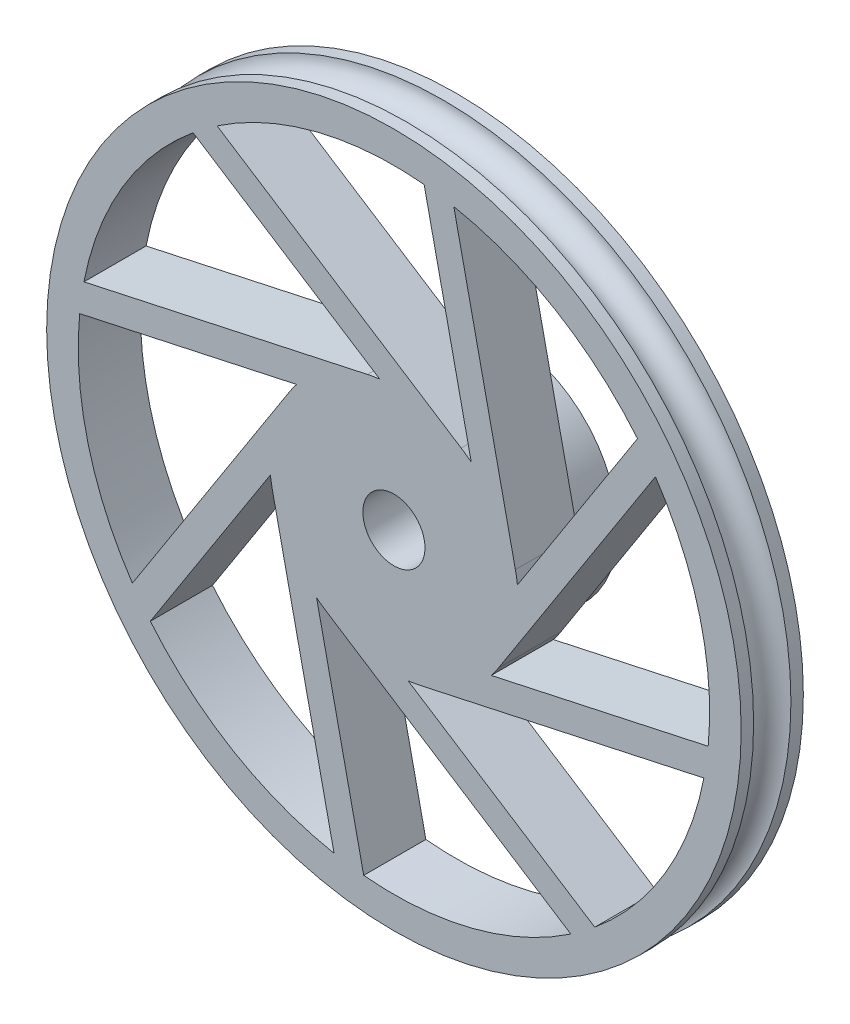
SolidWorks part; units mm, degrees
ref_plane "Front Plane" through (0, 0, 0) normal (0, 0, 1) x (1, 0, 0)
ref_plane "Top Plane" through (0, 0, 0) normal (0, 1, 0) x (1, 0, 0)
ref_plane "Right Plane" through (0, 0, 0) normal (1, 0, 0) x (0, 0, -1)
sketch "Sketch1" plane through (0, 0, 0) normal (0, 0, 1) x (1, 0, 0)
  circle A0 centre (0, 0) radius 27.94
  dimension "D1" = 55.88
extrude "Boss-Extrude1" add sketch "Sketch1" against normal blind 5 contours A0
sketch "Sketch6" plane through (0, 0, 0) normal (0, 1, 0) x (1, 0, 0)
  line L0 (27.94, 0) -> (27.94, 5) construction
  line L1 (5, 14.4799) -> (17.94, 14.4799)
  line L2 (5, 14.4799) -> (5, -9.1816)
  line L3 (5, -9.1816) -> (17.94, -9.1816)
  line L4 (17.94, 14.4799) -> (17.94, -9.1816)
  dimension "D1" = 5
  dimension "D2" = 10
ref_axis "Axis1" through (0, 0, -92.1481) along (0, 0, 1)
sketch "Sketch7" plane through (0, 0, 0) normal (0, 0, 1) x (1, 0, 0)
  line L0 (1.1353, -9.9354) -> (16.1586, -19.5974)
  line L1 (2.1224, -9.7722) -> (24.9391, -4.8167)
  line L2 (24.9391, -4.8167) -> (2.1224, -9.7722)
  line L3 (7.8281, -6.2226) -> (25.2833, -2.4316)
  line L4 (-5.4092, -8.4107) -> (14.2287, -21.0406)
  line L5 (-6.2226, -7.8281) -> (-2.4316, -25.2833)
  line L6 (-9.7722, -2.1224) -> (-4.8167, -24.9391)
  line L7 (-9.9354, -1.1353) -> (-19.5974, -16.1586)
  line L8 (-8.4107, 5.4092) -> (-21.0406, -14.2287)
  line L9 (-7.8281, 6.2226) -> (-25.2833, 2.4316)
  line L10 (-2.1224, 9.7722) -> (-24.9391, 4.8167)
  line L11 (-1.1353, 9.9354) -> (-16.1586, 19.5974)
  line L12 (5.4092, 8.4107) -> (-14.2287, 21.0406)
  line L13 (6.2226, 7.8281) -> (2.4316, 25.2833)
  line L14 (9.7722, 2.1224) -> (4.8167, 24.9391)
  line L15 (9.9354, 1.1353) -> (19.5974, 16.1586)
  line L16 (8.4107, -5.4092) -> (21.0406, 14.2287)
  line L17 (0, 0) -> (7.8281, -6.2226) construction
  circle A0 centre (0, 0) radius 10
  circle A1 centre (0, 0) radius 25.4
  dimension "D1" = 20
  dimension "D2" = 50.8
  dimension "D3" = 8
  dimension "D4" = 10
extrude "Cut-Extrude2" cut sketch "Sketch7" against normal blind 5 contours L5 A1 L4 | L0 A1 L1 | L3 A1 L16 | L15 A1 L14 | L13 A1 L12 | L11 A1 L10 | L9 A1 L8 | L7 A1 L6
sketch "Sketch9" plane through (0, 0, 0) normal (0, 1, 0) x (1, 0, 0)
  line L0 (-27.94, 5) -> (-27.94, 0) construction
  circle A0 centre (-27.94, 2.5) radius 1.5
  dimension "D1" = 3
revolve "Cut-Revolve3" cut sketch "Sketch9" angle 360 about axis through (0, 0, -92.1481) along (0, 0, 1)
sketch "Sketch10" plane through (0, 0, -5) normal (0, 0, -1) x (-1, 0, 0)
  circle A0 centre (0, 0) radius 9
  dimension "D1" = 18
extrude "Boss-Extrude2" add sketch "Sketch10" along normal blind 4
sketch "Sketch11" plane through (0, 0, -9) normal (0, 0, -1) x (-1, 0, 0)
  line L1 (7, 0) -> (3.5, 6.0622)
  line L2 (3.5, 6.0622) -> (-3.5, 6.0622)
  line L3 (-3.5, 6.0622) -> (-7, 0)
  line L4 (-7, 0) -> (-3.5, -6.0622)
  line L5 (-3.5, -6.0622) -> (3.5, -6.0622)
  line L6 (3.5, -6.0622) -> (7, 0)
  circle A0 centre (0, 0) radius 6.0622 construction
  dimension "D1" = 7
extrude "Cut-Extrude4" cut sketch "Sketch11" against normal blind 4
sketch "Sketch12" plane through (0, 0, -5) normal (0, 0, -1) x (-1, 0, 0)
  circle A0 centre (0, 0) radius 2.5
  dimension "D1" = 5
extrude "Cut-Extrude5" cut sketch "Sketch12" against normal through all
